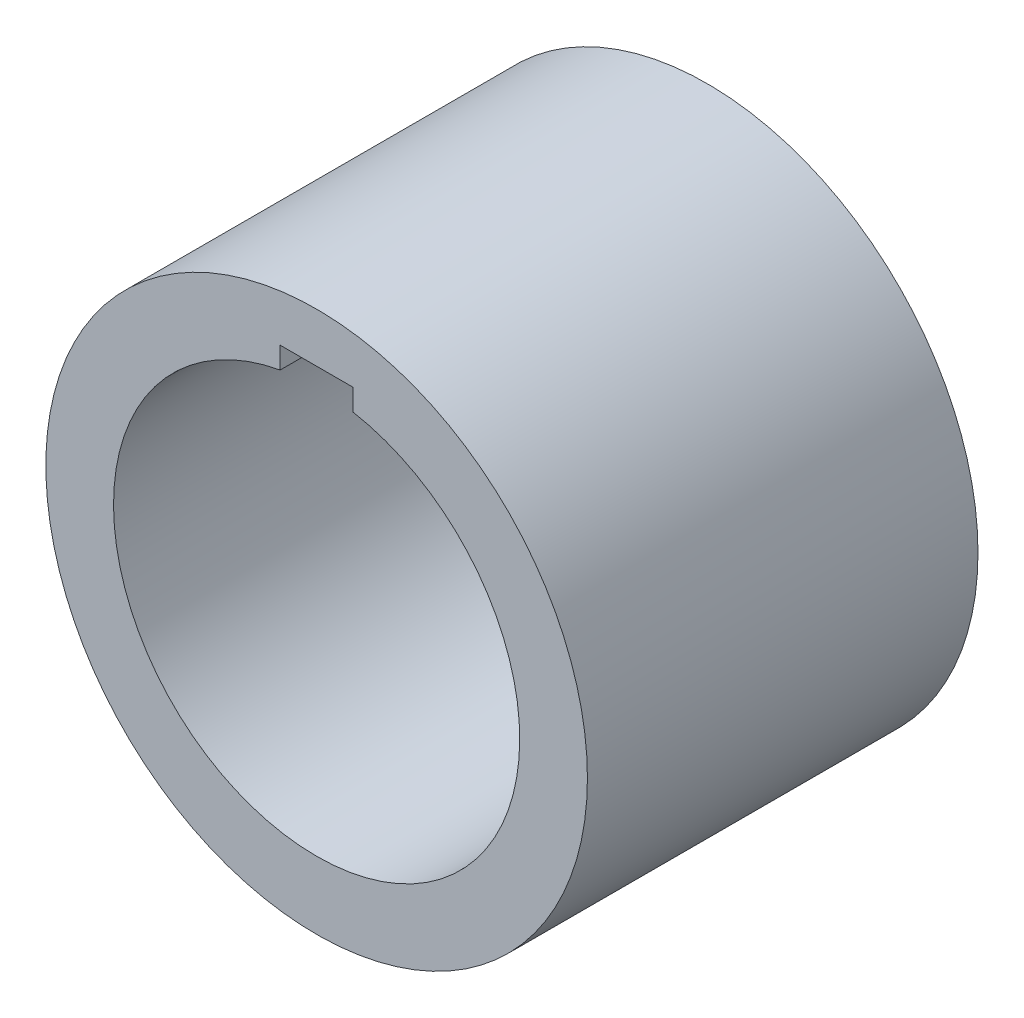
SolidWorks part; units mm, degrees
ref_plane "Front Plane" through (0, 0, 0) normal (0, 0, 1) x (1, 0, 0)
ref_plane "Top Plane" through (0, 0, 0) normal (0, 1, 0) x (1, 0, 0)
ref_plane "Right Plane" through (0, 0, 0) normal (1, 0, 0) x (0, 0, -1)
sketch "Sketch1" plane through (0, 0, 0) normal (0, 0, 1) x (1, 0, 0)
  circle A0 centre (0, 0) radius 10.4
  circle A1 centre (0, 0) radius 7.8
  dimension "D1" = 20.8
  dimension "D2" = 15.6
extrude "Boss-Extrude1" add sketch "Sketch1" along normal blind 15
sketch "Sketch2" plane through (0, 0, 15) normal (0, 0, 1) x (1, 0, 0)
  line L0 (0, 0) -> (0, 7.1) construction
  line L1 (1.4, 5.7) -> (-1.4, 5.7)
  line L2 (1.4, 5.7) -> (1.4, 8.5)
  line L3 (1.4, 8.5) -> (-1.4, 8.5)
  line L4 (-1.4, 5.7) -> (-1.4, 8.5)
  line L5 (1.4, 5.7) -> (-1.4, 8.5) construction
  line L6 (1.4, 8.5) -> (-1.4, 5.7) construction
  point P0 (0, 7.1)
  point P8 (0, 7.1)
  dimension "D1" = 2.8
  dimension "D2" = 8.5
extrude "Cut-Extrude1" cut sketch "Sketch2" against normal up to next
